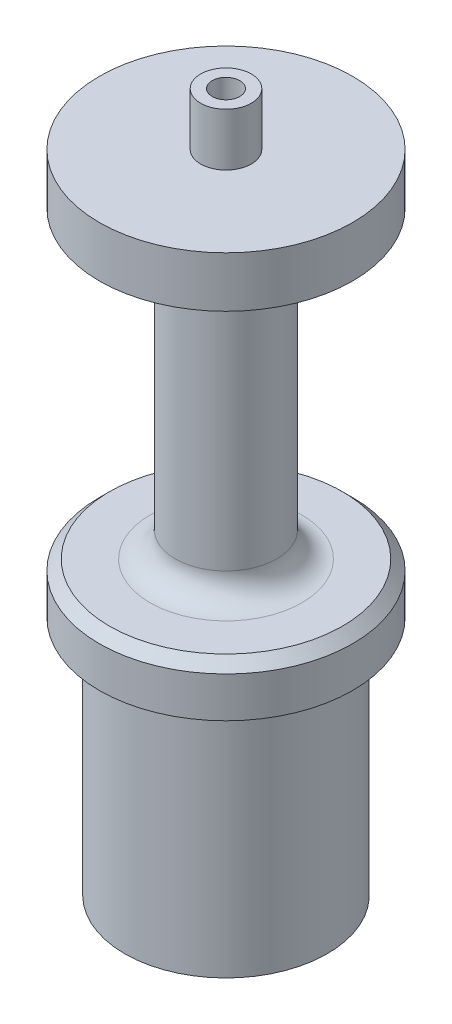
SolidWorks part; units mm, degrees
material "6061 Alloy"
ref_plane "Front Plane" through (0, 0, 0) normal (0, 0, 1) x (1, 0, 0)
ref_plane "Top Plane" through (0, 0, 0) normal (0, 1, 0) x (1, 0, 0)
ref_plane "Right Plane" through (0, 0, 0) normal (1, 0, 0) x (0, 0, -1)
sketch "Sketch1" plane through (0, 0, 0) normal (0, 1, 0) x (1, 0, 0)
  circle A0 centre (0, 0) radius 12.7
  dimension "D1" = 25.4
extrude "Boss-Extrude1" add sketch "Sketch1" along normal blind 30.1625
sketch "Sketch4" plane through (0, 30.1625, 0) normal (0, 1, 0) x (1, 0, 0)
  circle A0 centre (0, 0) radius 15.875
  dimension "D1" = 31.75
extrude "Boss-Extrude2" add sketch "Sketch4" along normal blind 50.8 contours A0
sketch "Sketch2" plane through (0, 0, 0) normal (0, -1, 0) x (1, 0, 0)
  line L0 (-8.777, 1.1225) -> (-1.1225, 8.777)
  line L1 (-5.4125, -7) -> (5.4125, -7)
  line L2 (-7, -5.4125) -> (-7, 5.4125)
  line L3 (-5.4125, 7) -> (5.4125, 7)
  line L4 (7, -5.4125) -> (7, 5.4125)
  line L5 (-7, -7) -> (7, 7) construction
  line L6 (-7, 7) -> (7, -7) construction
  line L7 (-8.777, -1.1225) -> (-1.1225, -8.777)
  line L8 (1.1225, 8.777) -> (8.777, 1.1225)
  line L9 (1.1225, -8.777) -> (8.777, -1.1225)
  line L10 (-9.8995, 0) -> (9.8995, 0) construction
  line L11 (0, 9.8995) -> (0, -9.8995) construction
  circle A0 centre (0, 0) radius 9 construction
  arc A1 (-8.777, 1.1225) -> (-8.777, -1.1225) centre (-7.6544, 0) ccw
  arc A2 (-7, -5.4125) -> (-5.4125, -7) centre (-5.4125, -5.4125) ccw
  arc A3 (-1.1225, -8.777) -> (1.1225, -8.777) centre (0, -7.6544) ccw
  arc A4 (5.4125, -7) -> (7, -5.4125) centre (5.4125, -5.4125) ccw
  arc A5 (8.777, -1.1225) -> (8.777, 1.1225) centre (7.6544, 0) ccw
  arc A6 (7, 5.4125) -> (5.4125, 7) centre (5.4125, 5.4125) ccw
  arc A7 (1.1225, 8.777) -> (-1.1225, 8.777) centre (0, 7.6544) ccw
  arc A8 (-5.4125, 7) -> (-7, 5.4125) centre (-5.4125, 5.4125) ccw
  point P0 (0, 0)
  point P7 (0, 0)
  dimension "D2" = 18
  dimension "D3" = 1.5875
  dimension "D1" = 14
extrude "Cut-Extrude1" cut sketch "Sketch2" against normal blind 11.176 contours L0 A1 L7 L2 | L1 L9 L4 L8 L3 L0 L2 L7 | L3 A8 L2 L0 | L8 A7 L0 L3 | L4 A6 L3 L8 | L9 A5 L8 L4 | L1 A4 L4 L9 | L7 A3 L9 L1 | L2 A2 L1 L7
sketch "Sketch3" plane through (0, 11.176, 0) normal (0, -1, 0) x (1, 0, 0)
  circle A0 centre (0, 0) radius 6
  dimension "D1" = 12
extrude "Cut-Extrude2" cut sketch "Sketch3" against normal blind 8
sketch "Sketch5" plane through (0, 80.9625, 0) normal (0, 1, 0) x (1, 0, 0)
  circle A0 centre (0, 0) radius 3.175
  dimension "D1" = 6.35
extrude "Boss-Extrude3" add sketch "Sketch5" along normal blind 6.604
hole_wizard "#8-32 Tapped Hole1" positions "Sketch6" profile "Sketch8" tap size "#8-32" standard "ANSI Inch" end condition through all
sketch "Sketch6" plane through (0, 87.5665, 0) normal (0, 1, 0) x (1, 0, 0)
  point P0 (0, 0)
sketch "Sketch8" plane through (0, 87.5665, 0) normal (1, 0, 0) x (0, 0, 1)
  line L0 (0, 0) -> (0, 87.5665)
  line L1 (0, 87.5665) -> (1.7272, 87.5665)
  line L2 (1.7272, 87.5665) -> (1.7272, 0)
  line L5 (1.7272, 0) -> (0, 0)
  line L11 (0, -6.35) -> (0, 107.95) construction
  dimension "Thru Tap Drill Dia." = 3.4544
  dimension "Thru Tap Drill Depth" = 87.5665
cosmetic thread "Hole Thread1" parameters "D2"=4.1656
sketch "Sketch9" plane through (0, 80.9625, 0) normal (0, 1, 0) x (1, 0, 0)
  circle A0 centre (0, 0) radius 15.875 construction
  circle A1 centre (0, 0) radius 15.875
  circle A2 centre (0, 0) radius 6.35
  dimension "D1" = 12.7
extrude "Cut-Extrude3" cut sketch "Sketch9" against normal blind 38.1 from offset 6.35 offset against normal yes
fillet "Fillet1" radius 3.175 2 edges at (0, 74.6125, 6.35) (0, 36.5125, 6.35)
chamfer "Chamfer1" distance 1.27 angle 45 1 edges at (0, 36.5125, 15.875)
